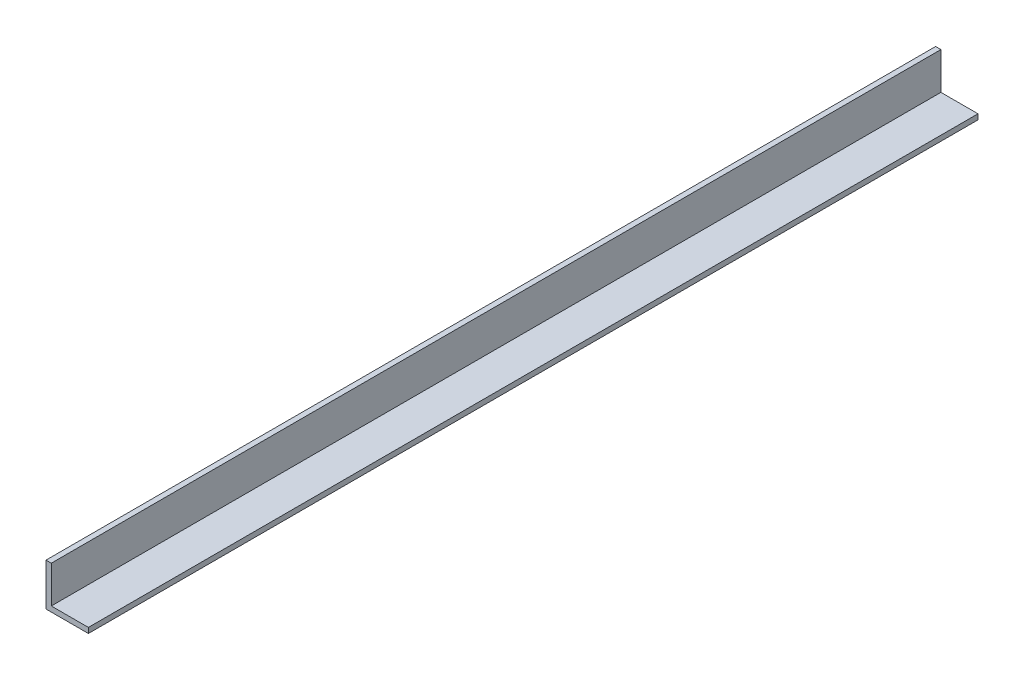
SolidWorks part; units mm, degrees
ref_plane "Front Plane" through (0, 0, 0) normal (0, 0, 1) x (1, 0, 0)
ref_plane "Top Plane" through (0, 0, 0) normal (0, 1, 0) x (1, 0, 0)
ref_plane "Right Plane" through (0, 0, 0) normal (1, 0, 0) x (0, 0, -1)
sketch "Sketch1" plane through (0, 0, 0) normal (0, 0, 1) x (1, 0, 0)
  line L0 (0, 25.4) -> (0, 0) construction
  line L1 (0, 0) -> (25.4, 0) construction
  line L2 (25.4, 0) -> (25.4, 3.175) construction
  line L3 (25.4, 3.175) -> (3.175, 3.175) construction
  line L4 (3.175, 3.175) -> (3.175, 25.4) construction
  line L6 (3.175, 25.4) -> (0, 25.4) construction
  arc A0 (3.175, 3.5814) -> (3.5814, 3.175) centre (3.5814, 3.5814) ccw construction
  point P4 (0, 0)
  dimension "Inside Corner Radius" = 0.4064
  dimension "Outside Height" = 25.4
  dimension "Inside Height" = 22.225
  dimension "Outside Width" = 25.4
  dimension "Inside Width" = 22.225
  dimension "Wall Thickness" = 3.175
  dimension "Shape" = 90
sketch "Sketch2" plane through (0, 0, 0) normal (1, 0, 0) x (0, 0, -1)
  line L0 (1219.2, 0) -> (-1219.2, 0) construction
  line L1 (-1219.2, 25.4) -> (-1219.2, 0) construction
  line L2 (1219.2, 25.4) -> (1219.2, 0) construction
  point P0 (-1189.99, 0)
  point P4 (0, 0)
  point P6 (1189.99, 0)
  dimension "D1" = 29.21
  dimension "D2" = 29.21
  dimension "D3" = 25.4
  dimension "Length" = 2438.4
sketch "Sketch3" plane through (0, 0, 0) normal (0, 0, 1) x (1, 0, 0)
  line L0 (3.175, 25.4) -> (0, 25.4)
  line L1 (0, 25.4) -> (0, 0)
  line L2 (0, 0) -> (25.4, 0)
  line L3 (25.4, 0) -> (25.4, 3.175)
  line L4 (25.4, 3.175) -> (3.175, 3.175)
  line L5 (3.175, 3.175) -> (3.175, 25.4)
extrude "Boss-Extrude1" add sketch "Sketch3" along normal mid plane 2438.4
fillet "Fillet1" radius 0.4064 1 edges at (3.175, 3.175, 0)
sketch "Sketch4" plane through (0, 0, 0) normal (-1, 0, 0) x (0, 0, 1)
  line L0 (1219.2, 25.4) -> (1219.2, 0) construction
  line L1 (-1219.2, 25.4) -> (686, 25.4)
  line L2 (-1219.2, 25.4) -> (-1219.2, -77.8785)
  line L3 (-1219.2, -77.8785) -> (686, -77.8785)
  line L4 (686, 25.4) -> (686, -77.8785)
  dimension "D1" = 533.2
extrude "Cut-Extrude1" cut sketch "Sketch4" against normal blind 60
sketch "Sketch5" plane through (0, 0, 686) normal (0, 0, -1) x (-1, 0, 0)
  line L0 (-3.175, 3.5814) -> (-3.175, 25.4) construction
  line L1 (-3.175, 6.1219) -> (-5.652, 6.1219)
  line L2 (-3.175, 6.1219) -> (-3.175, 3.175)
  line L3 (-3.175, 3.175) -> (-5.652, 3.175)
  line L4 (-5.652, 6.1219) -> (-5.652, 3.175)
  line L5 (-25.4, 3.175) -> (-3.5814, 3.175) construction
extrude "Cut-Extrude2" cut sketch "Sketch5" against normal blind 600
equation "\"D1@Boss-Extrude1\"=\"Length@Sketch2\""
equation "\"D1@Sketch2\" = \"Outside Width@Sketch1\" * 1.15"
equation "\"D2@Sketch2\"=\"D1@Sketch2\""
equation "\"D1@Fillet1\"=\"Inside Corner Radius@Sketch1\""
equation "\"D3@Sketch2\"=\"Outside Height@Sketch1\""
